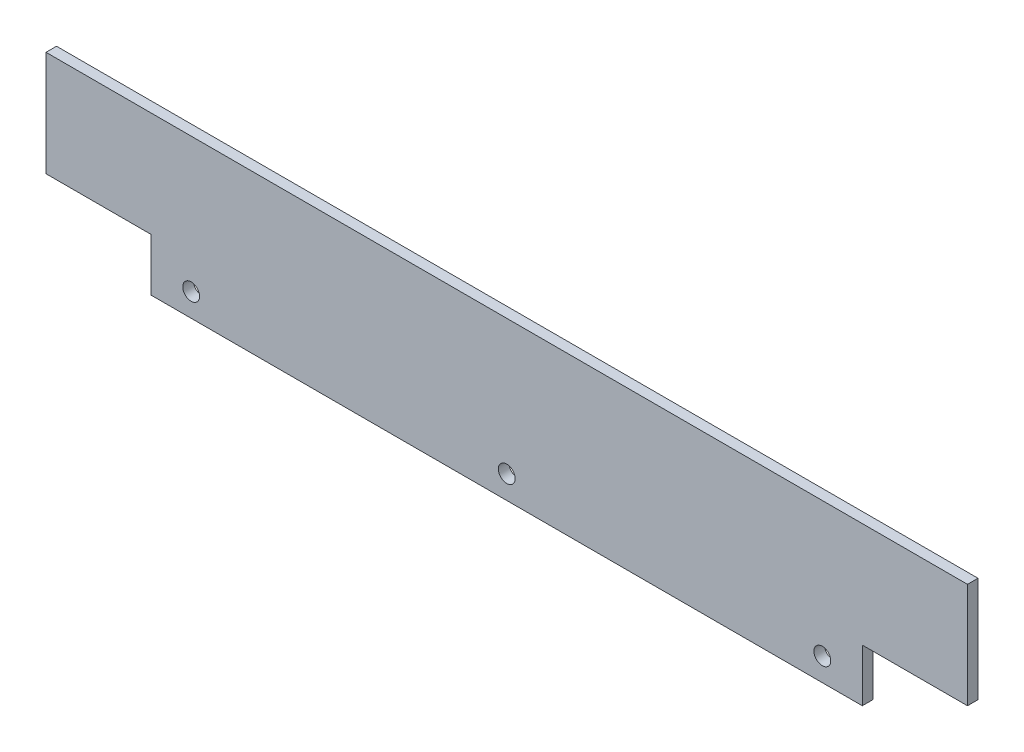
SolidWorks part; units mm, degrees
ref_plane "Alzado" through (0, 0, 0) normal (0, 0, 1) x (1, 0, 0)
ref_plane "Planta" through (0, 0, 0) normal (0, 1, 0) x (1, 0, 0)
ref_plane "Vista lateral" through (0, 0, 0) normal (1, 0, 0) x (0, 0, -1)
sketch "Croquis1" plane through (0, 0, 0) normal (0, 0, 1) x (1, 0, 0)
  line L0 (0, 0) -> (-338, 0)
  line L1 (-338, 0) -> (-338, 25)
  line L2 (-338, 25) -> (-388, 25)
  line L3 (-388, 25) -> (-388, 75)
  line L4 (-388, 75) -> (50, 75)
  line L5 (50, 75) -> (50, 25)
  line L6 (50, 25) -> (0, 25)
  line L7 (0, 25) -> (0, 0)
  line L8 (415.9078, 25) -> (-728.0032, 25) construction
  line L9 (44.691, 11) -> (-362.5608, 11) construction
  line L11 (-169, 75) -> (-169, -50.4144) construction
  circle A0 centre (-319, 11) radius 4
  circle A1 centre (-219, 11) radius 4 construction
  circle A2 centre (-119, 11) radius 4 construction
  circle A3 centre (-19, 11) radius 4
  circle A4 centre (-169, 11) radius 4
  dimension "D12" = 8
  dimension "D1" = 338
  dimension "D2" = 25
  dimension "D3" = 50
  dimension "D4" = 50
  dimension "D5" = 50
  dimension "D6" = 11
  dimension "D9" = 100
  dimension "D10" = 100
  dimension "D11" = 100
  dimension "D18" = 50
extrude "Saliente-Extruir1" add sketch "Croquis1" along normal blind 5
